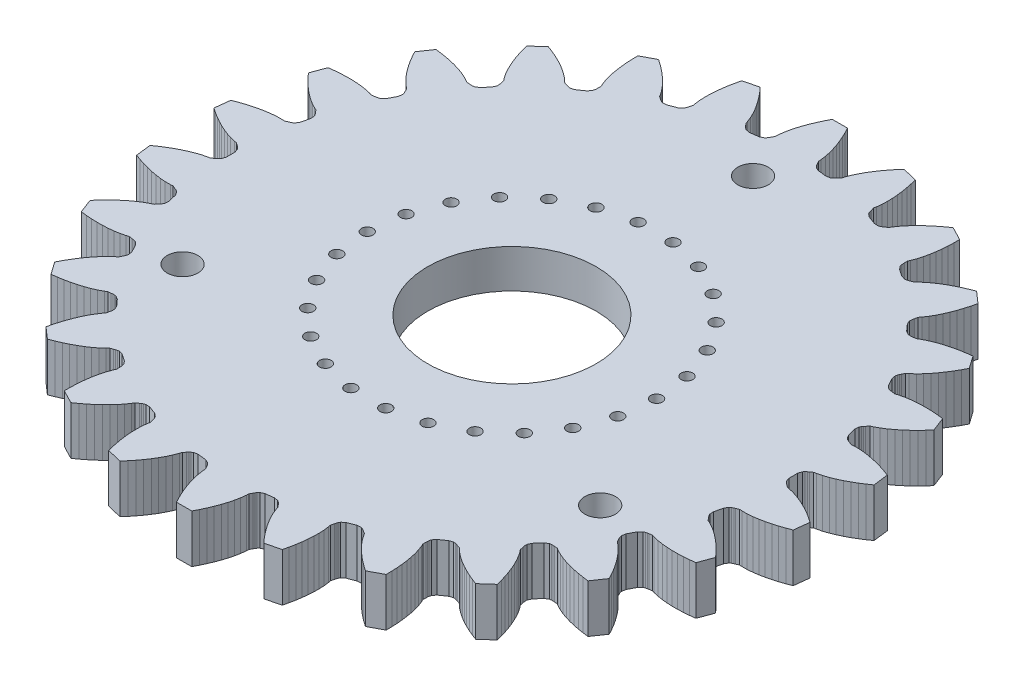
SolidWorks part; units mm, degrees
material "1060 Alloy"
ref_plane "Front Plane" through (0, 0, 0) normal (0, 0, 1) x (1, 0, 0)
ref_plane "Top Plane" through (0, 0, 0) normal (0, 1, 0) x (1, 0, 0)
ref_plane "Right Plane" through (0, 0, 0) normal (1, 0, 0) x (0, 0, -1)
sketch "Sketch1" plane through (0, 0, 0) normal (0, 1, 0) x (1, 0, 0)
  line L0 (0, 0) -> (54.8903, 0) construction
  line L1 (0, 0) -> (47.5263, 11.7142) construction
  line L2 (0, 0) -> (29.6137, 7.2991)
  line L3 (0, 0) -> (32, 0)
  circle A0 centre (0, 0) radius 32 construction
  circle A1 centre (0, 0) radius 30.5 construction
  arc A2 (29.6137, 7.2991) -> (32, 0) centre (21.3514, 0.5583) cw
  circle A3 centre (0, 0) radius 31.25 construction
  dimension "D1" = 62.5
  dimension "D2" = 1.5
  dimension "D4" = 0.75
  dimension "D3" = 13.846
extrude "Extrude ratchet edge" add sketch "Sketch1" along normal blind 10
pattern_circular "Pattern edge to form gear" count 26 over 360 about axis through (0, 0, 0) along (0, 1, 0) of "Extrude ratchet edge"
sketch "Sketch7" plane through (0, 10, 0) normal (0, 1, 0) x (1, 0, 0)
  circle A0 centre (0, 0) radius 8.7313
  dimension "D1" = 17.4625
sketch "Sketch12" plane through (0, 0, 0) normal (0, -1, 0) x (1, 0, 0)
  line L0 (29.0003, -0.6166) -> (29.1196, -1.0003)
  line L1 (29.1196, -1.0003) -> (29.244, -1.1506)
  line L2 (29.244, -1.1506) -> (29.3694, -1.2597)
  line L3 (29.3694, -1.2597) -> (29.4955, -1.346)
  line L4 (29.4955, -1.346) -> (29.7463, -1.5351)
  line L5 (29.7463, -1.5351) -> (30.0039, -1.5796)
  line L6 (30.0039, -1.5796) -> (30.5166, -1.7122)
  line L7 (30.5166, -1.7122) -> (31.0266, -1.8861)
  line L8 (31.0266, -1.8861) -> (31.5336, -2.0936)
  line L9 (31.5336, -2.0936) -> (32.0376, -2.3308)
  line L10 (32.0376, -2.3308) -> (32.5381, -2.595)
  line L11 (32.5381, -2.595) -> (33.035, -2.8848)
  line L12 (33.035, -2.8848) -> (33.5277, -3.1987)
  line L13 (33.5277, -3.1987) -> (34.0159, -3.5359)
  line L14 (34.0159, -3.5359) -> (33.8164, -5.1042)
  line L15 (33.8164, -5.1042) -> (33.2594, -5.3084)
  line L16 (33.2594, -5.3084) -> (32.7038, -5.4891)
  line L17 (32.7038, -5.4891) -> (32.1503, -5.6453)
  line L18 (32.1503, -5.6453) -> (31.5995, -5.7759)
  line L19 (31.5995, -5.7759) -> (31.0523, -5.8793)
  line L20 (31.0523, -5.8793) -> (30.5094, -5.9534)
  line L21 (30.5094, -5.9534) -> (29.9722, -5.9942)
  line L22 (29.9722, -5.9942) -> (29.4426, -5.9942)
  line L23 (29.4426, -5.9942) -> (29.182, -5.9728)
  line L24 (29.182, -5.9728) -> (28.8919, -6.0931)
  line L25 (28.8919, -6.0931) -> (28.7482, -6.1452)
  line L26 (28.7482, -6.1452) -> (28.5995, -6.2194)
  line L27 (28.5995, -6.2194) -> (28.4414, -6.3338)
  line L28 (28.4414, -6.3338) -> (28.2299, -6.6755)
  line L29 (28.2299, -6.6755) -> (28.0119, -7.539)
  line L30 (28.0119, -7.539) -> (28.0359, -7.9401)
  line L31 (28.0359, -7.9401) -> (28.1207, -8.1159)
  line L32 (28.1207, -8.1159) -> (28.2164, -8.2517)
  line L33 (28.2164, -8.2517) -> (28.3182, -8.3658)
  line L34 (28.3182, -8.3658) -> (28.5164, -8.6094)
  line L35 (28.5164, -8.6094) -> (28.7559, -8.7142)
  line L36 (28.7559, -8.7142) -> (29.222, -8.9657)
  line L37 (29.222, -8.9657) -> (29.6755, -9.2566)
  line L38 (29.6755, -9.2566) -> (30.1181, -9.5794)
  line L39 (30.1181, -9.5794) -> (30.5507, -9.9303)
  line L40 (30.5507, -9.9303) -> (30.9735, -10.3067)
  line L41 (30.9735, -10.3067) -> (31.3865, -10.7069)
  line L42 (31.3865, -10.7069) -> (31.7898, -11.1296)
  line L43 (31.7898, -11.1296) -> (32.1831, -11.5738)
  line L44 (32.1831, -11.5738) -> (31.6141, -13.0488)
  line L45 (31.6141, -13.0488) -> (31.0244, -13.1138)
  line L46 (31.0244, -13.1138) -> (30.4418, -13.1563)
  line L47 (30.4418, -13.1563) -> (29.8669, -13.1754)
  line L48 (29.8669, -13.1754) -> (29.3009, -13.1704)
  line L49 (29.3009, -13.1704) -> (28.7448, -13.1399)
  line L50 (28.7448, -13.1399) -> (28.2, -13.0819)
  line L51 (28.2, -13.0819) -> (27.6686, -12.9929)
  line L52 (27.6686, -12.9929) -> (27.1544, -12.8663)
  line L53 (27.1544, -12.8663) -> (26.9065, -12.7831)
  line L54 (26.9065, -12.7831) -> (26.5961, -12.8305)
  line L55 (26.5961, -12.8305) -> (26.4441, -12.8467)
  line L56 (26.4441, -12.8467) -> (26.2819, -12.8831)
  line L57 (26.2819, -12.8831) -> (26.1011, -12.9564)
  line L58 (26.1011, -12.9564) -> (25.814, -13.2375)
  line L59 (25.814, -13.2375) -> (25.3956, -14.0238)
  line L60 (25.3956, -14.0238) -> (25.3229, -14.4189)
  line L61 (25.3229, -14.4189) -> (25.3632, -14.6099)
  line L62 (25.3632, -14.6099) -> (25.4236, -14.7647)
  line L63 (25.4236, -14.7647) -> (25.4951, -14.8998)
  line L64 (25.4951, -14.8998) -> (25.6292, -15.1838)
  line L65 (25.6292, -15.1838) -> (25.8367, -15.3428)
  line L66 (25.8367, -15.3428) -> (26.2291, -15.6985)
  line L67 (26.2291, -15.6985) -> (26.5998, -16.0895)
  line L68 (26.5998, -16.0895) -> (26.9523, -16.5089)
  line L69 (26.9523, -16.5089) -> (27.2883, -16.9531)
  line L70 (27.2883, -16.9531) -> (27.6087, -17.4197)
  line L71 (27.6087, -17.4197) -> (27.914, -17.9072)
  line L72 (27.914, -17.9072) -> (28.2044, -18.4141)
  line L73 (28.2044, -18.4141) -> (28.48, -18.9395)
  line L74 (28.48, -18.9395) -> (27.5746, -20.2355)
  line L75 (27.5746, -20.2355) -> (26.9864, -20.1575)
  line L76 (26.9864, -20.1575) -> (26.4105, -20.0593)
  line L77 (26.4105, -20.0593) -> (25.8478, -19.9403)
  line L78 (25.8478, -19.9403) -> (25.2994, -19.8)
  line L79 (25.2994, -19.8) -> (24.7668, -19.6373)
  line L80 (24.7668, -19.6373) -> (24.2517, -19.4506)
  line L81 (24.2517, -19.4506) -> (23.7571, -19.237)
  line L82 (23.7571, -19.237) -> (23.2881, -18.991)
  line L83 (23.2881, -18.991) -> (23.0673, -18.8509)
  line L84 (23.0673, -18.8509) -> (22.7546, -18.8226)
  line L85 (22.7546, -18.8226) -> (22.6031, -18.802)
  line L86 (22.6031, -18.802) -> (22.4369, -18.7985)
  line L87 (22.4369, -18.7985) -> (22.2438, -18.8264)
  line L88 (22.2438, -18.8264) -> (21.8978, -19.0306)
  line L89 (21.8978, -19.0306) -> (21.3034, -19.694)
  line L90 (21.3034, -19.694) -> (21.1383, -20.0602)
  line L91 (21.1383, -20.0602) -> (21.1316, -20.2553)
  line L92 (21.1316, -20.2553) -> (21.1532, -20.4201)
  line L93 (21.1532, -20.4201) -> (21.1903, -20.5684)
  line L94 (21.1903, -20.5684) -> (21.2526, -20.8761)
  line L95 (21.2526, -20.8761) -> (21.416, -21.0803)
  line L96 (21.416, -21.0803) -> (21.7119, -21.5195)
  line L97 (21.7119, -21.5195) -> (21.9782, -21.9879)
  line L98 (21.9782, -21.9879) -> (22.2201, -22.4794)
  line L99 (22.2201, -22.4794) -> (22.4401, -22.9911)
  line L100 (22.4401, -22.9911) -> (22.6395, -23.5209)
  line L101 (22.6395, -23.5209) -> (22.8193, -24.0672)
  line L102 (22.8193, -24.0672) -> (22.9799, -24.6289)
  line L103 (22.9799, -24.6289) -> (23.1217, -25.205)
  line L104 (23.1217, -25.205) -> (21.9325, -26.2467)
  line L105 (21.9325, -26.2467) -> (21.3801, -26.0302)
  line L106 (21.3801, -26.0302) -> (20.8445, -25.797)
  line L107 (20.8445, -25.797) -> (20.3266, -25.5468)
  line L108 (20.3266, -25.5468) -> (19.8277, -25.2793)
  line L109 (19.8277, -25.2793) -> (19.3494, -24.9939)
  line L110 (19.3494, -24.9939) -> (18.894, -24.6893)
  line L111 (18.894, -24.6893) -> (18.4649, -24.3636)
  line L112 (18.4649, -24.3636) -> (18.0684, -24.0125)
  line L113 (18.0684, -24.0125) -> (17.8876, -23.8237)
  line L114 (17.8876, -23.8237) -> (17.5907, -23.7213)
  line L115 (17.5907, -23.7213) -> (17.4485, -23.665)
  line L116 (17.4485, -23.665) -> (17.288, -23.6219)
  line L117 (17.288, -23.6219) -> (17.0938, -23.6028)
  line L118 (17.0938, -23.6028) -> (16.709, -23.7182)
  line L119 (16.709, -23.7182) -> (15.9732, -24.22)
  line L120 (15.9732, -24.22) -> (15.7251, -24.5362)
  line L121 (15.7251, -24.5362) -> (15.672, -24.7239)
  line L122 (15.672, -24.7239) -> (15.6536, -24.8891)
  line L123 (15.6536, -24.8891) -> (15.6541, -25.042)
  line L124 (15.6541, -25.042) -> (15.641, -25.3558)
  line L125 (15.641, -25.3558) -> (15.7507, -25.593)
  line L126 (15.7507, -25.593) -> (15.9329, -26.0903)
  line L127 (15.9329, -26.0903) -> (16.0794, -26.6088)
  line L128 (16.0794, -26.6088) -> (16.1966, -27.144)
  line L129 (16.1966, -27.144) -> (16.2878, -27.6934)
  line L130 (16.2878, -27.6934) -> (16.3546, -28.2555)
  line L131 (16.3546, -28.2555) -> (16.3984, -28.829)
  line L132 (16.3984, -28.829) -> (16.4199, -29.4128)
  line L133 (16.4199, -29.4128) -> (16.4198, -30.0061)
  line L134 (16.4198, -30.0061) -> (15.0158, -30.7329)
  line L135 (15.0158, -30.7329) -> (14.5313, -30.3905)
  line L136 (14.5313, -30.3905) -> (14.067, -30.0359)
  line L137 (14.067, -30.0359) -> (13.624, -29.6691)
  line L138 (13.624, -29.6691) -> (13.2037, -29.29)
  line L139 (13.2037, -29.29) -> (12.8076, -28.8984)
  line L140 (12.8076, -28.8984) -> (12.4383, -28.4937)
  line L141 (12.4383, -28.4937) -> (12.0996, -28.0747)
  line L142 (12.0996, -28.0747) -> (11.7986, -27.6389)
  line L143 (11.7986, -27.6389) -> (11.6683, -27.4123)
  line L144 (11.6683, -27.4123) -> (11.4045, -27.2419)
  line L145 (11.4045, -27.2419) -> (11.28, -27.1532)
  line L146 (11.28, -27.1532) -> (11.1345, -27.0729)
  line L147 (11.1345, -27.0729) -> (10.9505, -27.0079)
  line L148 (10.9505, -27.0079) -> (10.5492, -27.0279)
  line L149 (10.5492, -27.0279) -> (9.7146, -27.339)
  line L150 (9.7146, -27.339) -> (9.3982, -27.5866)
  line L151 (9.3982, -27.5866) -> (9.3017, -27.7562)
  line L152 (9.3017, -27.7562) -> (9.2442, -27.9122)
  line L153 (9.2442, -27.9122) -> (9.2082, -28.0607)
  line L154 (9.2082, -28.0607) -> (9.1203, -28.3622)
  line L155 (9.1203, -28.3622) -> (9.1701, -28.6189)
  line L156 (9.1701, -28.6189) -> (9.2279, -29.1453)
  line L157 (9.2279, -29.1453) -> (9.2461, -29.6838)
  line L158 (9.2461, -29.6838) -> (9.2319, -30.2315)
  line L159 (9.2319, -30.2315) -> (9.1888, -30.7868)
  line L160 (9.1888, -30.7868) -> (9.1192, -31.3485)
  line L161 (9.1192, -31.3485) -> (9.0245, -31.9158)
  line L162 (9.0245, -31.9158) -> (8.9057, -32.4878)
  line L163 (8.9057, -32.4878) -> (8.7636, -33.0638)
  line L164 (8.7636, -33.0638) -> (7.2264, -33.4335)
  line L165 (7.2264, -33.4335) -> (6.8379, -32.9851)
  line L166 (6.8379, -32.9851) -> (6.472, -32.5297)
  line L167 (6.472, -32.5297) -> (6.1297, -32.0675)
  line L168 (6.1297, -32.0675) -> (5.8123, -31.5988)
  line L169 (5.8123, -31.5988) -> (5.5215, -31.1238)
  line L170 (5.5215, -31.1238) -> (5.2598, -30.6425)
  line L171 (5.2598, -30.6425) -> (5.0311, -30.1547)
  line L172 (5.0311, -30.1547) -> (4.8432, -29.6595)
  line L173 (4.8432, -29.6595) -> (4.7709, -29.4083)
  line L174 (4.7709, -29.4083) -> (4.5555, -29.1797)
  line L175 (4.5555, -29.1797) -> (4.4559, -29.0638)
  line L176 (4.4559, -29.0638) -> (4.3338, -28.951)
  line L177 (4.3338, -28.951) -> (4.1707, -28.8438)
  line L178 (4.1707, -28.8438) -> (3.7763, -28.7672)
  line L179 (3.7763, -28.7672) -> (2.8915, -28.8696)
  line L180 (2.8915, -28.8696) -> (2.525, -29.0342)
  line L181 (2.525, -29.0342) -> (2.3907, -29.1758)
  line L182 (2.3907, -29.1758) -> (2.2976, -29.3135)
  line L183 (2.2976, -29.3135) -> (2.2271, -29.4491)
  line L184 (2.2271, -29.4491) -> (2.0696, -29.7208)
  line L185 (2.0696, -29.7208) -> (2.0565, -29.9819)
  line L186 (2.0565, -29.9819) -> (1.9867, -30.5069)
  line L187 (1.9867, -30.5069) -> (1.8755, -31.0341)
  line L188 (1.8755, -31.0341) -> (1.7306, -31.5624)
  line L189 (1.7306, -31.5624) -> (1.5559, -32.0913)
  line L190 (1.5559, -32.0913) -> (1.3539, -32.6201)
  line L191 (1.3539, -32.6201) -> (1.1262, -33.1482)
  line L192 (1.1262, -33.1482) -> (0.8739, -33.6752)
  line L193 (0.8739, -33.6752) -> (0.5981, -34.2004)
  line L194 (0.5981, -34.2004) -> (-0.9829, -34.1915)
  line L195 (-0.9829, -34.1915) -> (-1.2528, -33.6632)
  line L196 (-1.2528, -33.6632) -> (-1.499, -33.1334)
  line L197 (-1.499, -33.1334) -> (-1.7208, -32.6027)
  line L198 (-1.7208, -32.6027) -> (-1.9169, -32.0717)
  line L199 (-1.9169, -32.0717) -> (-2.0855, -31.5409)
  line L200 (-2.0855, -31.5409) -> (-2.2244, -31.011)
  line L201 (-2.2244, -31.011) -> (-2.3297, -30.4826)
  line L202 (-2.3297, -30.4826) -> (-2.3936, -29.9568)
  line L203 (-2.3936, -29.9568) -> (-2.4037, -29.6956)
  line L204 (-2.4037, -29.6956) -> (-2.5581, -29.4221)
  line L205 (-2.5581, -29.4221) -> (-2.6272, -29.2857)
  line L206 (-2.6272, -29.2857) -> (-2.7187, -29.147)
  line L207 (-2.7187, -29.147) -> (-2.8514, -29.0039)
  line L208 (-2.8514, -29.0039) -> (-3.216, -28.8351)
  line L209 (-3.216, -28.8351) -> (-4.0996, -28.7228)
  line L210 (-4.0996, -28.7228) -> (-4.4948, -28.7949)
  line L211 (-4.4948, -28.7949) -> (-4.6591, -28.9003)
  line L212 (-4.6591, -28.9003) -> (-4.7824, -29.0117)
  line L213 (-4.7824, -29.0117) -> (-4.8834, -29.1265)
  line L214 (-4.8834, -29.1265) -> (-5.1013, -29.3526)
  line L215 (-5.1013, -29.3526) -> (-5.1765, -29.603)
  line L216 (-5.1765, -29.603) -> (-5.37, -30.096)
  line L217 (-5.37, -30.096) -> (-5.6041, -30.5812)
  line L218 (-5.6041, -30.5812) -> (-5.8712, -31.0596)
  line L219 (-5.8712, -31.0596) -> (-6.1674, -31.5313)
  line L220 (-6.1674, -31.5313) -> (-6.4901, -31.9963)
  line L221 (-6.4901, -31.9963) -> (-6.8376, -32.4546)
  line L222 (-6.8376, -32.4546) -> (-7.2086, -32.9059)
  line L223 (-7.2086, -32.9059) -> (-7.6021, -33.3499)
  line L224 (-7.6021, -33.3499) -> (-9.135, -32.9629)
  line L225 (-9.135, -32.9629) -> (-9.2706, -32.3853)
  line L226 (-9.2706, -32.3853) -> (-9.383, -31.812)
  line L227 (-9.383, -31.812) -> (-9.4713, -31.2437)
  line L228 (-9.4713, -31.2437) -> (-9.5346, -30.6812)
  line L229 (-9.5346, -30.6812) -> (-9.5713, -30.1254)
  line L230 (-9.5713, -30.1254) -> (-9.5793, -29.5776)
  line L231 (-9.5793, -29.5776) -> (-9.5551, -29.0394)
  line L232 (-9.5551, -29.0394) -> (-9.4913, -28.5136)
  line L233 (-9.4913, -28.5136) -> (-9.4387, -28.2576)
  line L234 (-9.4387, -28.2576) -> (-9.5231, -27.9551)
  line L235 (-9.5231, -27.9551) -> (-9.5575, -27.8061)
  line L236 (-9.5575, -27.8061) -> (-9.6132, -27.6496)
  line L237 (-9.6132, -27.6496) -> (-9.7078, -27.4789)
  line L238 (-9.7078, -27.4789) -> (-10.0214, -27.2277)
  line L239 (-10.0214, -27.2277) -> (-10.8524, -26.9072)
  line L240 (-10.8524, -26.9072) -> (-11.2535, -26.8827)
  line L241 (-11.2535, -26.8827) -> (-11.4382, -26.9456)
  line L242 (-11.4382, -26.9456) -> (-11.5846, -27.0243)
  line L243 (-11.5846, -27.0243) -> (-11.7101, -27.1116)
  line L244 (-11.7101, -27.1116) -> (-11.9758, -27.279)
  line L245 (-11.9758, -27.279) -> (-12.1087, -27.5041)
  line L246 (-12.1087, -27.5041) -> (-12.4145, -27.9365)
  line L247 (-12.4145, -27.9365) -> (-12.758, -28.3516)
  line L248 (-12.758, -28.3516) -> (-13.1318, -28.7521)
  line L249 (-13.1318, -28.7521) -> (-13.5322, -29.1392)
  line L250 (-13.5322, -29.1392) -> (-13.9568, -29.5135)
  line L251 (-13.9568, -29.5135) -> (-14.4039, -29.8753)
  line L252 (-14.4039, -29.8753) -> (-14.8722, -30.2247)
  line L253 (-14.8722, -30.2247) -> (-15.3605, -30.5616)
  line L254 (-15.3605, -30.5616) -> (-16.7562, -29.819)
  line L255 (-16.7562, -29.819) -> (-16.7497, -29.2258)
  line L256 (-16.7497, -29.2258) -> (-16.7216, -28.6422)
  line L257 (-16.7216, -28.6422) -> (-16.6713, -28.0693)
  line L258 (-16.6713, -28.0693) -> (-16.5981, -27.508)
  line L259 (-16.5981, -27.508) -> (-16.5008, -26.9596)
  line L260 (-16.5008, -26.9596) -> (-16.3775, -26.4258)
  line L261 (-16.3775, -26.4258) -> (-16.2252, -25.909)
  line L262 (-16.2252, -25.909) -> (-16.0374, -25.4138)
  line L263 (-16.0374, -25.4138) -> (-15.925, -25.1778)
  line L264 (-15.925, -25.1778) -> (-15.9346, -24.8639)
  line L265 (-15.9346, -24.8639) -> (-15.9324, -24.711)
  line L266 (-15.9324, -24.711) -> (-15.949, -24.5456)
  line L267 (-15.949, -24.5456) -> (-15.9999, -24.3573)
  line L268 (-15.9999, -24.3573) -> (-16.2444, -24.0384)
  line L269 (-16.2444, -24.0384) -> (-16.9745, -23.5283)
  line L270 (-16.9745, -23.5283) -> (-17.358, -23.4085)
  line L271 (-17.358, -23.4085) -> (-17.5524, -23.4254)
  line L272 (-17.5524, -23.4254) -> (-17.7134, -23.4668)
  line L273 (-17.7134, -23.4668) -> (-17.8562, -23.5215)
  line L274 (-17.8562, -23.5215) -> (-18.1542, -23.6204)
  line L275 (-18.1542, -23.6204) -> (-18.3371, -23.8072)
  line L276 (-18.3371, -23.8072) -> (-18.7375, -24.1538)
  line L277 (-18.7375, -24.1538) -> (-19.1704, -24.4747)
  line L278 (-19.1704, -24.4747) -> (-19.6292, -24.7741)
  line L279 (-19.6292, -24.7741) -> (-20.1106, -25.0541)
  line L280 (-20.1106, -25.0541) -> (-20.6125, -25.316)
  line L281 (-20.6125, -25.316) -> (-21.1332, -25.5603)
  line L282 (-21.1332, -25.5603) -> (-21.6714, -25.7874)
  line L283 (-21.6714, -25.7874) -> (-22.2262, -25.9977)
  line L284 (-22.2262, -25.9977) -> (-23.4036, -24.9426)
  line L285 (-23.4036, -24.9426) -> (-23.2553, -24.3682)
  line L286 (-23.2553, -24.3682) -> (-23.0883, -23.8083)
  line L287 (-23.0883, -23.8083) -> (-22.9024, -23.2641)
  line L288 (-22.9024, -23.2641) -> (-22.6971, -22.7366)
  line L289 (-22.6971, -22.7366) -> (-22.4713, -22.2274)
  line L290 (-22.4713, -22.2274) -> (-22.2239, -21.7386)
  line L291 (-22.2239, -21.7386) -> (-21.9523, -21.2733)
  line L292 (-21.9523, -21.2733) -> (-21.6515, -20.8374)
  line L293 (-21.6515, -20.8374) -> (-21.4858, -20.6352)
  line L294 (-21.4858, -20.6352) -> (-21.4201, -20.3281)
  line L295 (-21.4201, -20.3281) -> (-21.3813, -20.1802)
  line L296 (-21.3813, -20.1802) -> (-21.3578, -20.0157)
  line L297 (-21.3578, -20.0157) -> (-21.3622, -19.8206)
  line L298 (-21.3622, -19.8206) -> (-21.5232, -19.4525)
  line L299 (-21.5232, -19.4525) -> (-22.1101, -18.7825)
  line L300 (-22.1101, -18.7825) -> (-22.4538, -18.5744)
  line L301 (-22.4538, -18.5744) -> (-22.6466, -18.5443)
  line L302 (-22.6466, -18.5443) -> (-22.8128, -18.5459)
  line L303 (-22.8128, -18.5459) -> (-22.9645, -18.5648)
  line L304 (-22.9645, -18.5648) -> (-23.2775, -18.5896)
  line L305 (-23.2775, -18.5896) -> (-23.4999, -18.7272)
  line L306 (-23.4999, -18.7272) -> (-23.9716, -18.9679)
  line L307 (-23.9716, -18.9679) -> (-24.4686, -19.1758)
  line L308 (-24.4686, -19.1758) -> (-24.9858, -19.3568)
  line L309 (-24.9858, -19.3568) -> (-25.5202, -19.5135)
  line L310 (-25.5202, -19.5135) -> (-26.0702, -19.6476)
  line L311 (-26.0702, -19.6476) -> (-26.6342, -19.7602)
  line L312 (-26.6342, -19.7602) -> (-27.2111, -19.8519)
  line L313 (-27.2111, -19.8519) -> (-27.8001, -19.9233)
  line L314 (-27.8001, -19.9233) -> (-28.6909, -18.6171)
  line L315 (-28.6909, -18.6171) -> (-28.4094, -18.0949)
  line L316 (-28.4094, -18.0949) -> (-28.1133, -17.5912)
  line L317 (-28.1133, -17.5912) -> (-27.8025, -17.1073)
  line L318 (-27.8025, -17.1073) -> (-27.4769, -16.6443)
  line L319 (-27.4769, -16.6443) -> (-27.1359, -16.2039)
  line L320 (-27.1359, -16.2039) -> (-26.7786, -15.7885)
  line L321 (-26.7786, -15.7885) -> (-26.4036, -15.4018)
  line L322 (-26.4036, -15.4018) -> (-26.0072, -15.0505)
  line L323 (-26.0072, -15.0505) -> (-25.7979, -14.8938)
  line L324 (-25.7979, -14.8938) -> (-25.6606, -14.6114)
  line L325 (-25.6606, -14.6114) -> (-25.5876, -14.4771)
  line L326 (-25.5876, -14.4771) -> (-25.5254, -14.3229)
  line L327 (-25.5254, -14.3229) -> (-25.483, -14.1325)
  line L328 (-25.483, -14.1325) -> (-25.5512, -13.7365)
  line L329 (-25.5512, -13.7365) -> (-25.9607, -12.9455)
  line L330 (-25.9607, -12.9455) -> (-26.2446, -12.6612)
  line L331 (-26.2446, -12.6612) -> (-26.4246, -12.5859)
  line L332 (-26.4246, -12.5859) -> (-26.5864, -12.5476)
  line L333 (-26.5864, -12.5476) -> (-26.7382, -12.5297)
  line L334 (-26.7382, -12.5297) -> (-27.0481, -12.4789)
  line L335 (-27.0481, -12.4789) -> (-27.2968, -12.5592)
  line L336 (-27.2968, -12.5592) -> (-27.8125, -12.6801)
  line L337 (-27.8125, -12.6801) -> (-28.3448, -12.763)
  line L338 (-28.3448, -12.763) -> (-28.8902, -12.8149)
  line L339 (-28.8902, -12.8149) -> (-29.4467, -12.8392)
  line L340 (-29.4467, -12.8392) -> (-30.0127, -12.8378)
  line L341 (-30.0127, -12.8378) -> (-30.5873, -12.8121)
  line L342 (-30.5873, -12.8121) -> (-31.1694, -12.7631)
  line L343 (-31.1694, -12.7631) -> (-31.7584, -12.6915)
  line L344 (-31.7584, -12.6915) -> (-32.3107, -11.2101)
  line L345 (-32.3107, -11.2101) -> (-31.9124, -10.7704)
  line L346 (-31.9124, -10.7704) -> (-31.5044, -10.3522)
  line L347 (-31.5044, -10.3522) -> (-31.0868, -9.9567)
  line L348 (-31.0868, -9.9567) -> (-30.6598, -9.5851)
  line L349 (-30.6598, -9.5851) -> (-30.2233, -9.2392)
  line L350 (-30.2233, -9.2392) -> (-29.7771, -8.9214)
  line L351 (-29.7771, -8.9214) -> (-29.3203, -8.6356)
  line L352 (-29.3203, -8.6356) -> (-28.8514, -8.3894)
  line L353 (-28.8514, -8.3894) -> (-28.6108, -8.2873)
  line L354 (-28.6108, -8.2873) -> (-28.4098, -8.0459)
  line L355 (-28.4098, -8.0459) -> (-28.3068, -7.933)
  line L356 (-28.3068, -7.933) -> (-28.2095, -7.7982)
  line L357 (-28.2095, -7.7982) -> (-28.1228, -7.6234)
  line L358 (-28.1228, -7.6234) -> (-28.0943, -7.2226)
  line L359 (-28.0943, -7.2226) -> (-28.3025, -6.3567)
  line L360 (-28.3025, -6.3567) -> (-28.5102, -6.0127)
  line L361 (-28.5102, -6.0127) -> (-28.6669, -5.8964)
  line L362 (-28.6669, -5.8964) -> (-28.8148, -5.8206)
  line L363 (-28.8148, -5.8206) -> (-28.9579, -5.7669)
  line L364 (-28.9579, -5.7669) -> (-29.2466, -5.6433)
  line L365 (-29.2466, -5.6433) -> (-29.5074, -5.6618)
  line L366 (-29.5074, -5.6618) -> (-30.037, -5.6558)
  line L367 (-30.037, -5.6558) -> (-30.5737, -5.6089)
  line L368 (-30.5737, -5.6089) -> (-31.1157, -5.5288)
  line L369 (-31.1157, -5.5288) -> (-31.6618, -5.4192)
  line L370 (-31.6618, -5.4192) -> (-32.211, -5.2824)
  line L371 (-32.211, -5.2824) -> (-32.7628, -5.1199)
  line L372 (-32.7628, -5.1199) -> (-33.3163, -4.933)
  line L373 (-33.3163, -4.933) -> (-33.871, -4.7225)
  line L374 (-33.871, -4.7225) -> (-34.0527, -3.152)
  line L375 (-34.0527, -3.152) -> (-33.5607, -2.8204)
  line L376 (-33.5607, -2.8204) -> (-33.0645, -2.5121)
  line L377 (-33.0645, -2.5121) -> (-32.5644, -2.228)
  line L378 (-32.5644, -2.228) -> (-32.0609, -1.9693)
  line L379 (-32.0609, -1.9693) -> (-31.5543, -1.7379)
  line L380 (-31.5543, -1.7379) -> (-31.045, -1.5361)
  line L381 (-31.045, -1.5361) -> (-30.5331, -1.3679)
  line L382 (-30.5331, -1.3679) -> (-30.0189, -1.2411)
  line L383 (-30.0189, -1.2411) -> (-29.7608, -1.1996)
  line L384 (-29.7608, -1.1996) -> (-29.5079, -1.0133)
  line L385 (-29.5079, -1.0133) -> (-29.3809, -0.9284)
  line L386 (-29.3809, -0.9284) -> (-29.2542, -0.8208)
  line L387 (-29.2542, -0.8208) -> (-29.1281, -0.6718)
  line L388 (-29.1281, -0.6718) -> (-29.0045, -0.2895)
  line L389 (-29.0045, -0.2895) -> (-28.9995, 0.6011)
  line L390 (-28.9995, 0.6011) -> (-29.1188, 0.9848)
  line L391 (-29.1188, 0.9848) -> (-29.2432, 1.1352)
  line L392 (-29.2432, 1.1352) -> (-29.3686, 1.2442)
  line L393 (-29.3686, 1.2442) -> (-29.4947, 1.3306)
  line L394 (-29.4947, 1.3306) -> (-29.7455, 1.5197)
  line L395 (-29.7455, 1.5197) -> (-30.0031, 1.5641)
  line L396 (-30.0031, 1.5641) -> (-30.5158, 1.6968)
  line L397 (-30.5158, 1.6968) -> (-31.0257, 1.8707)
  line L398 (-31.0257, 1.8707) -> (-31.5328, 2.0782)
  line L399 (-31.5328, 2.0782) -> (-32.0368, 2.3153)
  line L400 (-32.0368, 2.3153) -> (-32.5373, 2.5796)
  line L401 (-32.5373, 2.5796) -> (-33.0342, 2.8694)
  line L402 (-33.0342, 2.8694) -> (-33.5269, 3.1833)
  line L403 (-33.5269, 3.1833) -> (-34.0151, 3.5204)
  line L404 (-34.0151, 3.5204) -> (-33.8156, 5.0888)
  line L405 (-33.8156, 5.0888) -> (-33.2586, 5.293)
  line L406 (-33.2586, 5.293) -> (-32.703, 5.4737)
  line L407 (-32.703, 5.4737) -> (-32.1495, 5.6298)
  line L408 (-32.1495, 5.6298) -> (-31.5987, 5.7604)
  line L409 (-31.5987, 5.7604) -> (-31.0515, 5.8639)
  line L410 (-31.0515, 5.8639) -> (-30.5086, 5.9379)
  line L411 (-30.5086, 5.9379) -> (-29.9714, 5.9787)
  line L412 (-29.9714, 5.9787) -> (-29.4418, 5.9788)
  line L413 (-29.4418, 5.9788) -> (-29.1812, 5.9574)
  line L414 (-29.1812, 5.9574) -> (-28.8911, 6.0777)
  line L415 (-28.8911, 6.0777) -> (-28.7474, 6.1298)
  line L416 (-28.7474, 6.1298) -> (-28.5987, 6.2039)
  line L417 (-28.5987, 6.2039) -> (-28.4406, 6.3184)
  line L418 (-28.4406, 6.3184) -> (-28.2291, 6.66)
  line L419 (-28.2291, 6.66) -> (-28.0111, 7.5236)
  line L420 (-28.0111, 7.5236) -> (-28.0351, 7.9247)
  line L421 (-28.0351, 7.9247) -> (-28.1199, 8.1004)
  line L422 (-28.1199, 8.1004) -> (-28.2156, 8.2363)
  line L423 (-28.2156, 8.2363) -> (-28.3174, 8.3504)
  line L424 (-28.3174, 8.3504) -> (-28.5156, 8.594)
  line L425 (-28.5156, 8.594) -> (-28.7551, 8.6988)
  line L426 (-28.7551, 8.6988) -> (-29.2212, 8.9502)
  line L427 (-29.2212, 8.9502) -> (-29.6746, 9.2412)
  line L428 (-29.6746, 9.2412) -> (-30.1173, 9.564)
  line L429 (-30.1173, 9.564) -> (-30.5499, 9.9148)
  line L430 (-30.5499, 9.9148) -> (-30.9727, 10.2912)
  line L431 (-30.9727, 10.2912) -> (-31.3857, 10.6914)
  line L432 (-31.3857, 10.6914) -> (-31.789, 11.1142)
  line L433 (-31.789, 11.1142) -> (-32.1823, 11.5583)
  line L434 (-32.1823, 11.5583) -> (-31.6133, 13.0334)
  line L435 (-31.6133, 13.0334) -> (-31.0236, 13.0984)
  line L436 (-31.0236, 13.0984) -> (-30.4409, 13.1408)
  line L437 (-30.4409, 13.1408) -> (-29.8661, 13.16)
  line L438 (-29.8661, 13.16) -> (-29.3001, 13.155)
  line L439 (-29.3001, 13.155) -> (-28.744, 13.1245)
  line L440 (-28.744, 13.1245) -> (-28.1992, 13.0665)
  line L441 (-28.1992, 13.0665) -> (-27.6678, 12.9775)
  line L442 (-27.6678, 12.9775) -> (-27.1536, 12.8508)
  line L443 (-27.1536, 12.8508) -> (-26.9057, 12.7677)
  line L444 (-26.9057, 12.7677) -> (-26.5953, 12.8151)
  line L445 (-26.5953, 12.8151) -> (-26.4433, 12.8312)
  line L446 (-26.4433, 12.8312) -> (-26.2811, 12.8676)
  line L447 (-26.2811, 12.8676) -> (-26.1002, 12.941)
  line L448 (-26.1002, 12.941) -> (-25.8131, 13.222)
  line L449 (-25.8131, 13.222) -> (-25.3948, 14.0083)
  line L450 (-25.3948, 14.0083) -> (-25.3221, 14.4035)
  line L451 (-25.3221, 14.4035) -> (-25.3623, 14.5945)
  line L452 (-25.3623, 14.5945) -> (-25.4228, 14.7493)
  line L453 (-25.4228, 14.7493) -> (-25.4943, 14.8844)
  line L454 (-25.4943, 14.8844) -> (-25.6284, 15.1683)
  line L455 (-25.6284, 15.1683) -> (-25.8359, 15.3274)
  line L456 (-25.8359, 15.3274) -> (-26.2283, 15.6831)
  line L457 (-26.2283, 15.6831) -> (-26.5989, 16.0741)
  line L458 (-26.5989, 16.0741) -> (-26.9515, 16.4935)
  line L459 (-26.9515, 16.4935) -> (-27.2875, 16.9377)
  line L460 (-27.2875, 16.9377) -> (-27.6079, 17.4043)
  line L461 (-27.6079, 17.4043) -> (-27.9132, 17.8917)
  line L462 (-27.9132, 17.8917) -> (-28.2036, 18.3987)
  line L463 (-28.2036, 18.3987) -> (-28.4792, 18.9241)
  line L464 (-28.4792, 18.9241) -> (-27.5738, 20.2201)
  line L465 (-27.5738, 20.2201) -> (-26.9856, 20.1421)
  line L466 (-26.9856, 20.1421) -> (-26.4097, 20.0438)
  line L467 (-26.4097, 20.0438) -> (-25.847, 19.9249)
  line L468 (-25.847, 19.9249) -> (-25.2986, 19.7846)
  line L469 (-25.2986, 19.7846) -> (-24.766, 19.6219)
  line L470 (-24.766, 19.6219) -> (-24.2509, 19.4351)
  line L471 (-24.2509, 19.4351) -> (-23.7562, 19.2216)
  line L472 (-23.7562, 19.2216) -> (-23.2873, 18.9756)
  line L473 (-23.2873, 18.9756) -> (-23.0665, 18.8355)
  line L474 (-23.0665, 18.8355) -> (-22.7538, 18.8072)
  line L475 (-22.7538, 18.8072) -> (-22.6023, 18.7865)
  line L476 (-22.6023, 18.7865) -> (-22.4361, 18.7831)
  line L477 (-22.4361, 18.7831) -> (-22.243, 18.811)
  line L478 (-22.243, 18.811) -> (-21.897, 19.0152)
  line L479 (-21.897, 19.0152) -> (-21.3026, 19.6785)
  line L480 (-21.3026, 19.6785) -> (-21.1374, 20.0448)
  line L481 (-21.1374, 20.0448) -> (-21.1308, 20.2399)
  line L482 (-21.1308, 20.2399) -> (-21.1524, 20.4046)
  line L483 (-21.1524, 20.4046) -> (-21.1895, 20.5529)
  line L484 (-21.1895, 20.5529) -> (-21.2518, 20.8607)
  line L485 (-21.2518, 20.8607) -> (-21.4152, 21.0648)
  line L486 (-21.4152, 21.0648) -> (-21.7111, 21.5041)
  line L487 (-21.7111, 21.5041) -> (-21.9774, 21.9724)
  line L488 (-21.9774, 21.9724) -> (-22.2193, 22.464)
  line L489 (-22.2193, 22.464) -> (-22.4393, 22.9757)
  line L490 (-22.4393, 22.9757) -> (-22.6387, 23.5054)
  line L491 (-22.6387, 23.5054) -> (-22.8185, 24.0518)
  line L492 (-22.8185, 24.0518) -> (-22.9791, 24.6135)
  line L493 (-22.9791, 24.6135) -> (-23.1209, 25.1896)
  line L494 (-23.1209, 25.1896) -> (-21.9317, 26.2312)
  line L495 (-21.9317, 26.2312) -> (-21.3793, 26.0148)
  line L496 (-21.3793, 26.0148) -> (-20.8436, 25.7815)
  line L497 (-20.8436, 25.7815) -> (-20.3258, 25.5314)
  line L498 (-20.3258, 25.5314) -> (-19.8269, 25.2639)
  line L499 (-19.8269, 25.2639) -> (-19.3486, 24.9785)
  line L500 (-19.3486, 24.9785) -> (-18.8932, 24.6739)
  line L501 (-18.8932, 24.6739) -> (-18.464, 24.3482)
  line L502 (-18.464, 24.3482) -> (-18.0676, 23.997)
  line L503 (-18.0676, 23.997) -> (-17.8868, 23.8082)
  line L504 (-17.8868, 23.8082) -> (-17.5899, 23.7059)
  line L505 (-17.5899, 23.7059) -> (-17.4477, 23.6496)
  line L506 (-17.4477, 23.6496) -> (-17.2872, 23.6065)
  line L507 (-17.2872, 23.6065) -> (-17.093, 23.5873)
  line L508 (-17.093, 23.5873) -> (-16.7082, 23.7028)
  line L509 (-16.7082, 23.7028) -> (-15.9723, 24.2046)
  line L510 (-15.9723, 24.2046) -> (-15.7243, 24.5207)
  line L511 (-15.7243, 24.5207) -> (-15.6712, 24.7085)
  line L512 (-15.6712, 24.7085) -> (-15.6528, 24.8737)
  line L513 (-15.6528, 24.8737) -> (-15.6533, 25.0266)
  line L514 (-15.6533, 25.0266) -> (-15.6401, 25.3403)
  line L515 (-15.6401, 25.3403) -> (-15.7499, 25.5776)
  line L516 (-15.7499, 25.5776) -> (-15.932, 26.0749)
  line L517 (-15.932, 26.0749) -> (-16.0786, 26.5934)
  line L518 (-16.0786, 26.5934) -> (-16.1958, 27.1285)
  line L519 (-16.1958, 27.1285) -> (-16.2869, 27.678)
  line L520 (-16.2869, 27.678) -> (-16.3538, 28.2401)
  line L521 (-16.3538, 28.2401) -> (-16.3976, 28.8136)
  line L522 (-16.3976, 28.8136) -> (-16.4191, 29.3974)
  line L523 (-16.4191, 29.3974) -> (-16.419, 29.9907)
  line L524 (-16.419, 29.9907) -> (-15.015, 30.7175)
  line L525 (-15.015, 30.7175) -> (-14.5305, 30.3751)
  line L526 (-14.5305, 30.3751) -> (-14.0662, 30.0205)
  line L527 (-14.0662, 30.0205) -> (-13.6232, 29.6536)
  line L528 (-13.6232, 29.6536) -> (-13.2028, 29.2746)
  line L529 (-13.2028, 29.2746) -> (-12.8068, 28.8829)
  line L530 (-12.8068, 28.8829) -> (-12.4375, 28.4782)
  line L531 (-12.4375, 28.4782) -> (-12.0988, 28.0593)
  line L532 (-12.0988, 28.0593) -> (-11.7978, 27.6235)
  line L533 (-11.7978, 27.6235) -> (-11.6675, 27.3969)
  line L534 (-11.6675, 27.3969) -> (-11.4037, 27.2265)
  line L535 (-11.4037, 27.2265) -> (-11.2792, 27.1378)
  line L536 (-11.2792, 27.1378) -> (-11.1336, 27.0575)
  line L537 (-11.1336, 27.0575) -> (-10.9497, 26.9924)
  line L538 (-10.9497, 26.9924) -> (-10.5484, 27.0125)
  line L539 (-10.5484, 27.0125) -> (-9.7138, 27.3236)
  line L540 (-9.7138, 27.3236) -> (-9.3974, 27.5712)
  line L541 (-9.3974, 27.5712) -> (-9.3009, 27.7408)
  line L542 (-9.3009, 27.7408) -> (-9.2434, 27.8967)
  line L543 (-9.2434, 27.8967) -> (-9.2073, 28.0453)
  line L544 (-9.2073, 28.0453) -> (-9.1195, 28.3468)
  line L545 (-9.1195, 28.3468) -> (-9.1693, 28.6034)
  line L546 (-9.1693, 28.6034) -> (-9.2271, 29.1299)
  line L547 (-9.2271, 29.1299) -> (-9.2453, 29.6683)
  line L548 (-9.2453, 29.6683) -> (-9.231, 30.216)
  line L549 (-9.231, 30.216) -> (-9.188, 30.7713)
  line L550 (-9.188, 30.7713) -> (-9.1184, 31.3331)
  line L551 (-9.1184, 31.3331) -> (-9.0237, 31.9004)
  line L552 (-9.0237, 31.9004) -> (-8.9049, 32.4724)
  line L553 (-8.9049, 32.4724) -> (-8.7628, 33.0484)
  line L554 (-8.7628, 33.0484) -> (-7.2256, 33.4181)
  line L555 (-7.2256, 33.4181) -> (-6.8371, 32.9697)
  line L556 (-6.8371, 32.9697) -> (-6.4712, 32.5142)
  line L557 (-6.4712, 32.5142) -> (-6.1289, 32.0521)
  line L558 (-6.1289, 32.0521) -> (-5.8115, 31.5834)
  line L559 (-5.8115, 31.5834) -> (-5.5207, 31.1084)
  line L560 (-5.5207, 31.1084) -> (-5.259, 30.6271)
  line L561 (-5.259, 30.6271) -> (-5.0303, 30.1392)
  line L562 (-5.0303, 30.1392) -> (-4.8424, 29.644)
  line L563 (-4.8424, 29.644) -> (-4.7701, 29.3928)
  line L564 (-4.7701, 29.3928) -> (-4.5547, 29.1643)
  line L565 (-4.5547, 29.1643) -> (-4.4551, 29.0483)
  line L566 (-4.4551, 29.0483) -> (-4.333, 28.9356)
  line L567 (-4.333, 28.9356) -> (-4.1699, 28.8284)
  line L568 (-4.1699, 28.8284) -> (-3.7755, 28.7518)
  line L569 (-3.7755, 28.7518) -> (-2.8907, 28.8541)
  line L570 (-2.8907, 28.8541) -> (-2.5242, 29.0188)
  line L571 (-2.5242, 29.0188) -> (-2.3899, 29.1604)
  line L572 (-2.3899, 29.1604) -> (-2.2968, 29.2981)
  line L573 (-2.2968, 29.2981) -> (-2.2263, 29.4337)
  line L574 (-2.2263, 29.4337) -> (-2.0688, 29.7054)
  line L575 (-2.0688, 29.7054) -> (-2.0557, 29.9665)
  line L576 (-2.0557, 29.9665) -> (-1.9859, 30.4915)
  line L577 (-1.9859, 30.4915) -> (-1.8747, 31.0186)
  line L578 (-1.8747, 31.0186) -> (-1.7298, 31.547)
  line L579 (-1.7298, 31.547) -> (-1.5551, 32.0759)
  line L580 (-1.5551, 32.0759) -> (-1.3531, 32.6047)
  line L581 (-1.3531, 32.6047) -> (-1.1254, 33.1328)
  line L582 (-1.1254, 33.1328) -> (-0.8731, 33.6597)
  line L583 (-0.8731, 33.6597) -> (-0.5973, 34.185)
  line L584 (-0.5973, 34.185) -> (0.9837, 34.1761)
  line L585 (0.9837, 34.1761) -> (1.2536, 33.6477)
  line L586 (1.2536, 33.6477) -> (1.4999, 33.118)
  line L587 (1.4999, 33.118) -> (1.7216, 32.5873)
  line L588 (1.7216, 32.5873) -> (1.9177, 32.0563)
  line L589 (1.9177, 32.0563) -> (2.0863, 31.5255)
  line L590 (2.0863, 31.5255) -> (2.2252, 30.9955)
  line L591 (2.2252, 30.9955) -> (2.3305, 30.4671)
  line L592 (2.3305, 30.4671) -> (2.3944, 29.9414)
  line L593 (2.3944, 29.9414) -> (2.4046, 29.6802)
  line L594 (2.4046, 29.6802) -> (2.5589, 29.4067)
  line L595 (2.5589, 29.4067) -> (2.628, 29.2703)
  line L596 (2.628, 29.2703) -> (2.7195, 29.1316)
  line L597 (2.7195, 29.1316) -> (2.8522, 28.9885)
  line L598 (2.8522, 28.9885) -> (3.2168, 28.8197)
  line L599 (3.2168, 28.8197) -> (4.1004, 28.7074)
  line L600 (4.1004, 28.7074) -> (4.4956, 28.7795)
  line L601 (4.4956, 28.7795) -> (4.6599, 28.8849)
  line L602 (4.6599, 28.8849) -> (4.7833, 28.9963)
  line L603 (4.7833, 28.9963) -> (4.8842, 29.111)
  line L604 (4.8842, 29.111) -> (5.1021, 29.3372)
  line L605 (5.1021, 29.3372) -> (5.1773, 29.5876)
  line L606 (5.1773, 29.5876) -> (5.3708, 30.0806)
  line L607 (5.3708, 30.0806) -> (5.6049, 30.5658)
  line L608 (5.6049, 30.5658) -> (5.872, 31.0441)
  line L609 (5.872, 31.0441) -> (6.1682, 31.5159)
  line L610 (6.1682, 31.5159) -> (6.4909, 31.9809)
  line L611 (6.4909, 31.9809) -> (6.8384, 32.4392)
  line L612 (6.8384, 32.4392) -> (7.2094, 32.8905)
  line L613 (7.2094, 32.8905) -> (7.6029, 33.3345)
  line L614 (7.6029, 33.3345) -> (9.1358, 32.9475)
  line L615 (9.1358, 32.9475) -> (9.2714, 32.3699)
  line L616 (9.2714, 32.3699) -> (9.3838, 31.7966)
  line L617 (9.3838, 31.7966) -> (9.4721, 31.2283)
  line L618 (9.4721, 31.2283) -> (9.5354, 30.6658)
  line L619 (9.5354, 30.6658) -> (9.5721, 30.11)
  line L620 (9.5721, 30.11) -> (9.5802, 29.5622)
  line L621 (9.5802, 29.5622) -> (9.5559, 29.024)
  line L622 (9.5559, 29.024) -> (9.4921, 28.4982)
  line L623 (9.4921, 28.4982) -> (9.4395, 28.2421)
  line L624 (9.4395, 28.2421) -> (9.5239, 27.9397)
  line L625 (9.5239, 27.9397) -> (9.5583, 27.7907)
  line L626 (9.5583, 27.7907) -> (9.614, 27.6341)
  line L627 (9.614, 27.6341) -> (9.7086, 27.4634)
  line L628 (9.7086, 27.4634) -> (10.0222, 27.2123)
  line L629 (10.0222, 27.2123) -> (10.8532, 26.8918)
  line L630 (10.8532, 26.8918) -> (11.2543, 26.8672)
  line L631 (11.2543, 26.8672) -> (11.439, 26.9302)
  line L632 (11.439, 26.9302) -> (11.5854, 27.0088)
  line L633 (11.5854, 27.0088) -> (11.7109, 27.0961)
  line L634 (11.7109, 27.0961) -> (11.9766, 27.2635)
  line L635 (11.9766, 27.2635) -> (12.1095, 27.4886)
  line L636 (12.1095, 27.4886) -> (12.4153, 27.921)
  line L637 (12.4153, 27.921) -> (12.7588, 28.3361)
  line L638 (12.7588, 28.3361) -> (13.1326, 28.7367)
  line L639 (13.1326, 28.7367) -> (13.533, 29.1238)
  line L640 (13.533, 29.1238) -> (13.9576, 29.4981)
  line L641 (13.9576, 29.4981) -> (14.4047, 29.8599)
  line L642 (14.4047, 29.8599) -> (14.873, 30.2093)
  line L643 (14.873, 30.2093) -> (15.3613, 30.5462)
  line L644 (15.3613, 30.5462) -> (16.757, 29.8036)
  line L645 (16.757, 29.8036) -> (16.7505, 29.2103)
  line L646 (16.7505, 29.2103) -> (16.7224, 28.6268)
  line L647 (16.7224, 28.6268) -> (16.6721, 28.0539)
  line L648 (16.6721, 28.0539) -> (16.5989, 27.4926)
  line L649 (16.5989, 27.4926) -> (16.5016, 26.9442)
  line L650 (16.5016, 26.9442) -> (16.3783, 26.4104)
  line L651 (16.3783, 26.4104) -> (16.226, 25.8936)
  line L652 (16.226, 25.8936) -> (16.0383, 25.3983)
  line L653 (16.0383, 25.3983) -> (15.9258, 25.1623)
  line L654 (15.9258, 25.1623) -> (15.9354, 24.8484)
  line L655 (15.9354, 24.8484) -> (15.9332, 24.6956)
  line L656 (15.9332, 24.6956) -> (15.9498, 24.5302)
  line L657 (15.9498, 24.5302) -> (16.0008, 24.3418)
  line L658 (16.0008, 24.3418) -> (16.2452, 24.023)
  line L659 (16.2452, 24.023) -> (16.9753, 23.5129)
  line L660 (16.9753, 23.5129) -> (17.3588, 23.3931)
  line L661 (17.3588, 23.3931) -> (17.5533, 23.41)
  line L662 (17.5533, 23.41) -> (17.7142, 23.4513)
  line L663 (17.7142, 23.4513) -> (17.857, 23.506)
  line L664 (17.857, 23.506) -> (18.155, 23.605)
  line L665 (18.155, 23.605) -> (18.3379, 23.7918)
  line L666 (18.3379, 23.7918) -> (18.7383, 24.1384)
  line L667 (18.7383, 24.1384) -> (19.1712, 24.4592)
  line L668 (19.1712, 24.4592) -> (19.63, 24.7587)
  line L669 (19.63, 24.7587) -> (20.1114, 25.0387)
  line L670 (20.1114, 25.0387) -> (20.6133, 25.3005)
  line L671 (20.6133, 25.3005) -> (21.134, 25.5448)
  line L672 (21.134, 25.5448) -> (21.6722, 25.772)
  line L673 (21.6722, 25.772) -> (22.227, 25.9822)
  line L674 (22.227, 25.9822) -> (23.4044, 24.9272)
  line L675 (23.4044, 24.9272) -> (23.2561, 24.3528)
  line L676 (23.2561, 24.3528) -> (23.0892, 23.7929)
  line L677 (23.0892, 23.7929) -> (22.9033, 23.2487)
  line L678 (22.9033, 23.2487) -> (22.6979, 22.7212)
  line L679 (22.6979, 22.7212) -> (22.4721, 22.212)
  line L680 (22.4721, 22.212) -> (22.2247, 21.7232)
  line L681 (22.2247, 21.7232) -> (21.9531, 21.2579)
  line L682 (21.9531, 21.2579) -> (21.6523, 20.822)
  line L683 (21.6523, 20.822) -> (21.4866, 20.6197)
  line L684 (21.4866, 20.6197) -> (21.4209, 20.3127)
  line L685 (21.4209, 20.3127) -> (21.3821, 20.1648)
  line L686 (21.3821, 20.1648) -> (21.3586, 20.0003)
  line L687 (21.3586, 20.0003) -> (21.363, 19.8052)
  line L688 (21.363, 19.8052) -> (21.5241, 19.437)
  line L689 (21.5241, 19.437) -> (22.1109, 18.767)
  line L690 (22.1109, 18.767) -> (22.4546, 18.5589)
  line L691 (22.4546, 18.5589) -> (22.6474, 18.5289)
  line L692 (22.6474, 18.5289) -> (22.8136, 18.5305)
  line L693 (22.8136, 18.5305) -> (22.9653, 18.5494)
  line L694 (22.9653, 18.5494) -> (23.2784, 18.5742)
  line L695 (23.2784, 18.5742) -> (23.5007, 18.7117)
  line L696 (23.5007, 18.7117) -> (23.9724, 18.9525)
  line L697 (23.9724, 18.9525) -> (24.4694, 19.1604)
  line L698 (24.4694, 19.1604) -> (24.9866, 19.3413)
  line L699 (24.9866, 19.3413) -> (25.521, 19.498)
  line L700 (25.521, 19.498) -> (26.071, 19.6321)
  line L701 (26.071, 19.6321) -> (26.635, 19.7447)
  line L702 (26.635, 19.7447) -> (27.2119, 19.8365)
  line L703 (27.2119, 19.8365) -> (27.8009, 19.9079)
  line L704 (27.8009, 19.9079) -> (28.6917, 18.6017)
  line L705 (28.6917, 18.6017) -> (28.4102, 18.0794)
  line L706 (28.4102, 18.0794) -> (28.1141, 17.5758)
  line L707 (28.1141, 17.5758) -> (27.8034, 17.0918)
  line L708 (27.8034, 17.0918) -> (27.4777, 16.6289)
  line L709 (27.4777, 16.6289) -> (27.1367, 16.1885)
  line L710 (27.1367, 16.1885) -> (26.7794, 15.7731)
  line L711 (26.7794, 15.7731) -> (26.4044, 15.3863)
  line L712 (26.4044, 15.3863) -> (26.008, 15.0351)
  line L713 (26.008, 15.0351) -> (25.7988, 14.8783)
  line L714 (25.7988, 14.8783) -> (25.6614, 14.5959)
  line L715 (25.6614, 14.5959) -> (25.5884, 14.4616)
  line L716 (25.5884, 14.4616) -> (25.5262, 14.3075)
  line L717 (25.5262, 14.3075) -> (25.4838, 14.117)
  line L718 (25.4838, 14.117) -> (25.5521, 13.7211)
  line L719 (25.5521, 13.7211) -> (25.9615, 12.9301)
  line L720 (25.9615, 12.9301) -> (26.2454, 12.6458)
  line L721 (26.2454, 12.6458) -> (26.4254, 12.5704)
  line L722 (26.4254, 12.5704) -> (26.5872, 12.5322)
  line L723 (26.5872, 12.5322) -> (26.739, 12.5143)
  line L724 (26.739, 12.5143) -> (27.0489, 12.4634)
  line L725 (27.0489, 12.4634) -> (27.2976, 12.5438)
  line L726 (27.2976, 12.5438) -> (27.8133, 12.6647)
  line L727 (27.8133, 12.6647) -> (28.3456, 12.7476)
  line L728 (28.3456, 12.7476) -> (28.8911, 12.7995)
  line L729 (28.8911, 12.7995) -> (29.4475, 12.8237)
  line L730 (29.4475, 12.8237) -> (30.0135, 12.8224)
  line L731 (30.0135, 12.8224) -> (30.5881, 12.7967)
  line L732 (30.5881, 12.7967) -> (31.1703, 12.7477)
  line L733 (31.1703, 12.7477) -> (31.7592, 12.676)
  line L734 (31.7592, 12.676) -> (32.3115, 11.1947)
  line L735 (32.3115, 11.1947) -> (31.9132, 10.755)
  line L736 (31.9132, 10.755) -> (31.5052, 10.3368)
  line L737 (31.5052, 10.3368) -> (31.0876, 9.9413)
  line L738 (31.0876, 9.9413) -> (30.6607, 9.5697)
  line L739 (30.6607, 9.5697) -> (30.2241, 9.2237)
  line L740 (30.2241, 9.2237) -> (29.7779, 8.9059)
  line L741 (29.7779, 8.9059) -> (29.3212, 8.6201)
  line L742 (29.3212, 8.6201) -> (28.8522, 8.3739)
  line L743 (28.8522, 8.3739) -> (28.6116, 8.2718)
  line L744 (28.6116, 8.2718) -> (28.4106, 8.0305)
  line L745 (28.4106, 8.0305) -> (28.3076, 7.9176)
  line L746 (28.3076, 7.9176) -> (28.2103, 7.7828)
  line L747 (28.2103, 7.7828) -> (28.1236, 7.608)
  line L748 (28.1236, 7.608) -> (28.0951, 7.2072)
  line L749 (28.0951, 7.2072) -> (28.3033, 6.3412)
  line L750 (28.3033, 6.3412) -> (28.511, 5.9973)
  line L751 (28.511, 5.9973) -> (28.6677, 5.881)
  line L752 (28.6677, 5.881) -> (28.8156, 5.8052)
  line L753 (28.8156, 5.8052) -> (28.9587, 5.7515)
  line L754 (28.9587, 5.7515) -> (29.2474, 5.6279)
  line L755 (29.2474, 5.6279) -> (29.5082, 5.6464)
  line L756 (29.5082, 5.6464) -> (30.0378, 5.6404)
  line L757 (30.0378, 5.6404) -> (30.5745, 5.5935)
  line L758 (30.5745, 5.5935) -> (31.1165, 5.5134)
  line L759 (31.1165, 5.5134) -> (31.6626, 5.4037)
  line L760 (31.6626, 5.4037) -> (32.2118, 5.2669)
  line L761 (32.2118, 5.2669) -> (32.7636, 5.1045)
  line L762 (32.7636, 5.1045) -> (33.3171, 4.9176)
  line L763 (33.3171, 4.9176) -> (33.8718, 4.7071)
  line L764 (33.8718, 4.7071) -> (34.0535, 3.1366)
  line L765 (34.0535, 3.1366) -> (33.5615, 2.805)
  line L766 (33.5615, 2.805) -> (33.0653, 2.4966)
  line L767 (33.0653, 2.4966) -> (32.5653, 2.2125)
  line L768 (32.5653, 2.2125) -> (32.0617, 1.9539)
  line L769 (32.0617, 1.9539) -> (31.5551, 1.7225)
  line L770 (31.5551, 1.7225) -> (31.0458, 1.5207)
  line L771 (31.0458, 1.5207) -> (30.5339, 1.3525)
  line L772 (30.5339, 1.3525) -> (30.0197, 1.2257)
  line L773 (30.0197, 1.2257) -> (29.7616, 1.1841)
  line L774 (29.7616, 1.1841) -> (29.5087, 0.9979)
  line L775 (29.5087, 0.9979) -> (29.3817, 0.9129)
  line L776 (29.3817, 0.9129) -> (29.255, 0.8053)
  line L777 (29.255, 0.8053) -> (29.1289, 0.6564)
  line L778 (29.1289, 0.6564) -> (29.0053, 0.2741)
  line L779 (29.0053, 0.2741) -> (29.0003, -0.6166)
extrude "Boss-Extrude1" add sketch "Sketch12" along normal blind 5
sketch "Sketch10" plane through (0, 10, 0) normal (0, 1, 0) x (1, 0, 0)
  line L0 (-0.7538, 29.3517) -> (-0.7538, 27.3517)
  line L1 (1.2462, 27.3517) -> (1.2462, 29.3517)
  line L2 (1.2462, 29.3517) -> (-0.7538, 29.3517)
  line L3 (0.2462, -0.1301) -> (0.2462, 41.1735) construction
  line L4 (0.2462, -0.1301) -> (0.2462, 36.6199) construction
  arc A0 (-0.7538, 27.3517) -> (1.2462, 27.3517) centre (0.2462, -0.1301) ccw
  dimension "D1" = 2
extrude "Cut-Extrude1" cut sketch "Sketch10" against normal blind 1
extrude "Cut bearing hole" cut sketch "Sketch7" against normal through all
sketch "Sketch11" plane through (0, -5, 0) normal (0, -1, 0) x (1, 0, 0)
  line L0 (1, -29.4818) -> (1, -27.4818)
  line L1 (-1, -27.4818) -> (-1, -29.4818)
  line L2 (-1, -29.4818) -> (1, -29.4818)
  line L3 (0, 0) -> (0, -100.666) construction
  arc A0 (1, -27.4818) -> (-1, -27.4818) centre (0, 0) ccw
  point P0 (0, -29.4818)
  dimension "D2" = 2
  dimension "D3" = 27.5
  dimension "D1" = 2
  dimension "D4" = 2
extrude "Cut-Extrude2" cut sketch "Sketch11" against normal blind 1
sketch "pin holes" plane through (0, 9, 0) normal (0, 1, 0) x (1, 0, 0)
  circle A0 centre (15, 0) radius 0.6
  circle A1 centre (14.5641, -3.5897) radius 0.6
  circle A2 centre (13.2818, -6.9708) radius 0.6
  circle A3 centre (11.2277, -9.9468) radius 0.6
  circle A4 centre (8.521, -12.3448) radius 0.6
  circle A5 centre (5.3191, -14.0252) radius 0.6
  circle A6 centre (1.8081, -14.8906) radius 0.6
  circle A7 centre (-1.8081, -14.8906) radius 0.6
  circle A8 centre (-5.3191, -14.0252) radius 0.6
  circle A9 centre (-8.521, -12.3448) radius 0.6
  circle A10 centre (-11.2277, -9.9468) radius 0.6
  circle A11 centre (-13.2818, -6.9708) radius 0.6
  circle A12 centre (-14.5641, -3.5897) radius 0.6
  circle A13 centre (-15, 0) radius 0.6
  circle A14 centre (-14.5641, 3.5897) radius 0.6
  circle A15 centre (-13.2818, 6.9708) radius 0.6
  circle A16 centre (-11.2277, 9.9468) radius 0.6
  circle A17 centre (-8.521, 12.3448) radius 0.6
  circle A18 centre (-5.3191, 14.0252) radius 0.6
  circle A19 centre (-1.8081, 14.8906) radius 0.6
  circle A20 centre (1.8081, 14.8906) radius 0.6
  circle A21 centre (5.3191, 14.0252) radius 0.6
  circle A22 centre (8.521, 12.3448) radius 0.6
  circle A23 centre (11.2277, 9.9468) radius 0.6
  circle A24 centre (13.2818, 6.9708) radius 0.6
  circle A25 centre (14.5641, 3.5897) radius 0.6
  point P55 (0, 0)
  dimension "D1" = 1.2
  dimension "D2" = 15
  dimension "D3" = 26
extrude "Pin holes cut" cut sketch "pin holes" against normal through all
sketch "Sketch13" plane through (0, -4, 0) normal (0, -1, 0) x (1, 0, 0)
  line L0 (0, 0) -> (0, -55.0487) construction
  circle A0 centre (0, -25) radius 1.5875
  circle A1 centre (-21.6506, 12.5) radius 1.5875
  circle A2 centre (21.6506, 12.5) radius 1.5875
  point P11 (0, 0)
  dimension "D1" = 3.175
  dimension "D2" = 25
  dimension "D3" = 3
extrude "Cut-Extrude3" cut sketch "Sketch13" against normal through all
sketch "Sketch14" plane through (0, 0, 0) normal (0, -1, 0) x (1, 0, 0)
  circle A0 centre (0, 0) radius 49.9868
extrude "Cut-Extrude4" cut sketch "Sketch14" against normal through all
equation "\"Bearing size\"= 17.4625mm"
equation "\"D1@Sketch7\" = \"Bearing size\""
equation "\"dedendum\"= 2mm"
equation "\"addendum\"= 2mm"
equation "\"D5@Iteration wheel\" = \"addendum\""
equation "\"base diameter\"=58"
equation "\"alpha\"= sqr ( ( \"base diameter\" + \"dedendum\" ) ^ 2 - \"base diameter\" ^ 2 ) / \"base diameter\" * 180 / PI - \"phi\""
equation "\"phi\"= 20"
